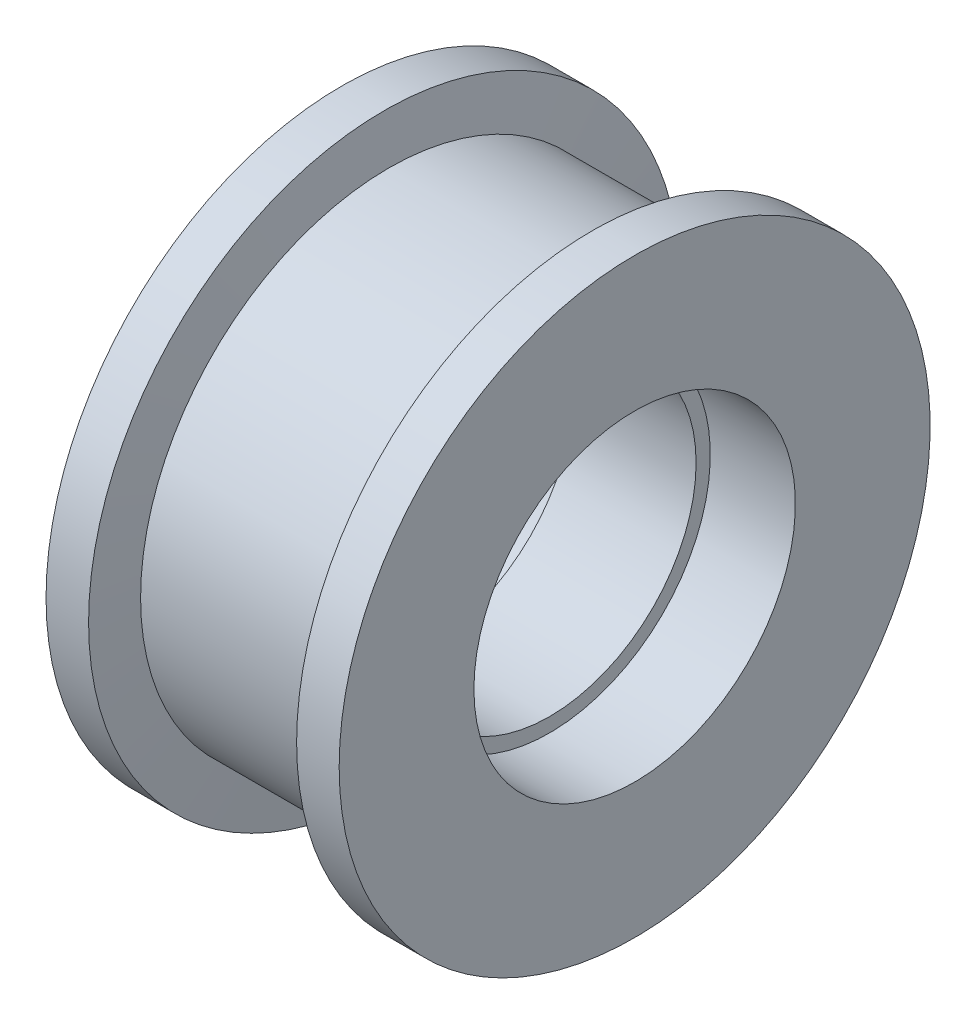
SolidWorks part; units mm, degrees
material "AISI 1045 钢，冷拔"
ref_plane "前视基准面" through (0, 0, 0) normal (0, 0, 1) x (1, 0, 0)
ref_plane "上视基准面" through (0, 0, 0) normal (0, 1, 0) x (1, 0, 0)
ref_plane "右视基准面" through (0, 0, 0) normal (1, 0, 0) x (0, 0, -1)
ref_plane "基准面4" through (0, 0, 0) normal (0, 1, 0) x (1, 0, 0)
sketch "草图2" plane through (0, 0, 0) normal (0, 1, 0) x (1, 0, 0)
  line L0 (-4235.1784, -7411.4832) -> (-4120.1784, -7411.4832) construction
  line L3 (-4202.9152, -7473.9832) -> (-4193.9152, -7473.9832)
  line L4 (-4193.9152, -7473.9832) -> (-4192.9152, -7463.9832)
  line L5 (-4192.9152, -7463.9832) -> (-4150.9152, -7463.9832)
  line L6 (-4150.9152, -7463.9832) -> (-4149.9152, -7473.9832)
  line L7 (-4149.9152, -7473.9832) -> (-4140.9152, -7473.9832)
  line L8 (-4140.9152, -7473.9832) -> (-4140.9152, -7445.4832)
  line L9 (-4140.9152, -7445.4832) -> (-4158.9152, -7445.4832)
  line L10 (-4158.9152, -7445.4832) -> (-4158.9152, -7442.4832)
  line L11 (-4158.9152, -7442.4832) -> (-4184.9152, -7442.4832)
  line L12 (-4184.9152, -7442.4832) -> (-4184.9152, -7445.4832)
  line L13 (-4184.9152, -7445.4832) -> (-4202.9152, -7445.4832)
  line L14 (-4202.9152, -7445.4832) -> (-4202.9152, -7473.9832)
  dimension "D1" = 34
  dimension "D2" = 18
  dimension "D3" = 18
  dimension "D4" = 9
  dimension "D5" = 10
  dimension "D6" = 52.5
  dimension "D7" = 10
  dimension "D8" = 9
  dimension "D9" = 10
  dimension "D10" = 10
  dimension "D11" = 42
  dimension "D12" = 3
  dimension "D13" = 3
revolve "旋转2" add sketch "草图2" angle 360 about L0
